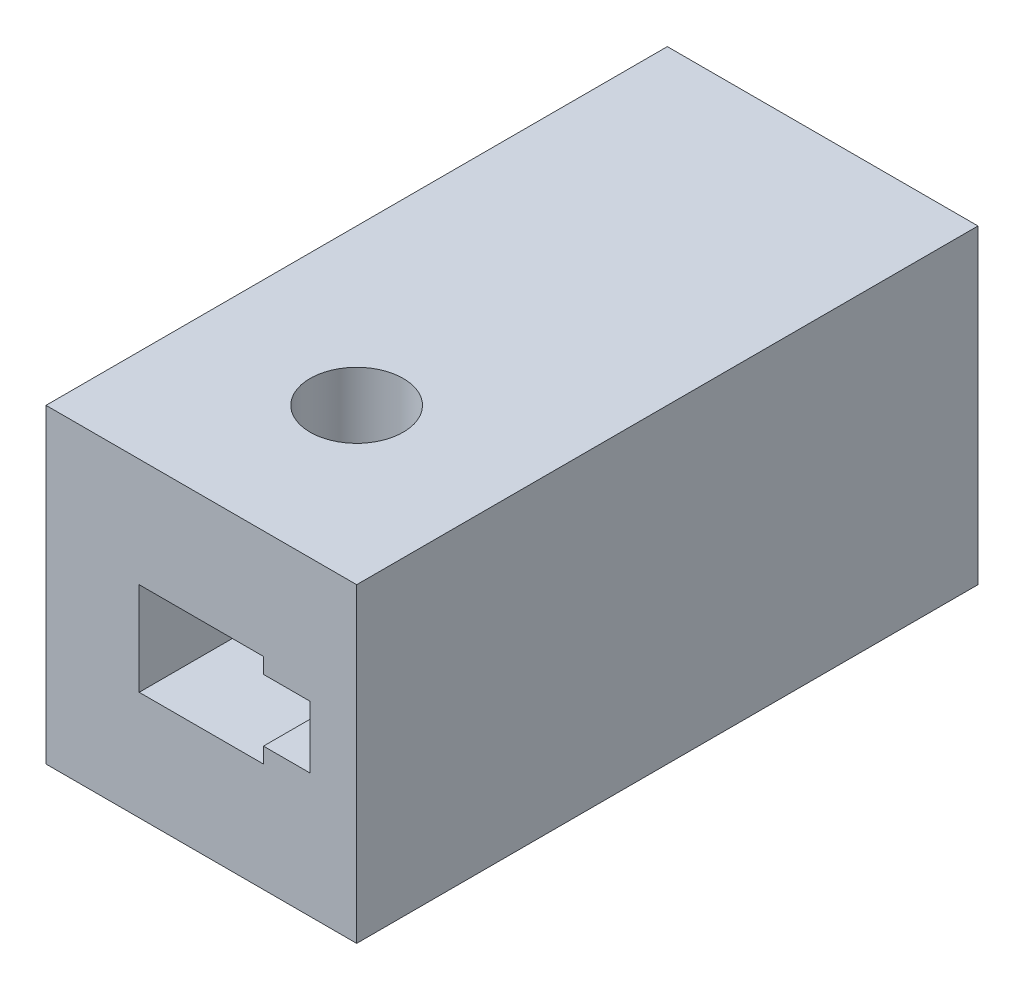
SolidWorks part; units mm, degrees
material "ABS"
ref_plane "Front Plane" through (0, 0, 0) normal (0, 0, 1) x (1, 0, 0)
ref_plane "Top Plane" through (0, 0, 0) normal (0, 1, 0) x (1, 0, 0)
ref_plane "Right Plane" through (0, 0, 0) normal (1, 0, 0) x (0, 0, -1)
sketch "Sketch1" plane through (0, 0, 0) normal (0, 0, 1) x (1, 0, 0)
  line L1 (-5, -5) -> (5, -5)
  line L2 (-5, -5) -> (-5, 5)
  line L3 (-5, 5) -> (5, 5)
  line L4 (5, -5) -> (5, 5)
  line L5 (-5, -5) -> (5, 5) construction
  line L6 (-5, 5) -> (5, -5) construction
  line L7 (-2, -1.5) -> (2, -1.5)
  line L8 (-2, -1.5) -> (-2, 1.5)
  line L9 (-2, 1.5) -> (2, 1.5)
  line L10 (2, -1.5) -> (2, 1.5)
  line L11 (-2, -1.5) -> (2, 1.5) construction
  line L12 (-2, 1.5) -> (2, -1.5) construction
  line L13 (2, -1) -> (3.5, -1)
  line L14 (2, -1) -> (2, 1)
  line L15 (2, 1) -> (3.5, 1)
  line L16 (3.5, -1) -> (3.5, 1)
  line L17 (2, -1) -> (3.5, 1) construction
  line L18 (2, 1) -> (3.5, -1) construction
  point P0 (0, 0)
  point P5 (0, 0)
  point P11 (2.75, 0)
  dimension "D1" = 10
  dimension "D2" = 10
  dimension "D3" = 4
  dimension "D4" = 3
  dimension "D5" = 2
  dimension "D6" = 1.5
  dimension "D7" = 0.75
  dimension "D8" = 1.5
extrude "Boss-Extrude1" add sketch "Sketch1" along normal blind 20 contours L1 L4 L3 L2 L16 L13 L10 L7 L8 L9 L15
sketch "Sketch2" plane through (0, -5, 0) normal (0, -1, 0) x (1, 0, 0)
  line L0 (-5, 20) -> (5, 20) construction
  circle A0 centre (0, 15) radius 1.5
  dimension "D1" = 3
  dimension "D2" = 5
extrude "Cut-Extrude1" cut sketch "Sketch2" against normal blind 20
sketch "Sketch3" plane through (0, 0, 0) normal (0, 0, -1) x (-1, 0, 0)
  line L1 (-5, -5) -> (5, -5)
  line L2 (-5, -5) -> (-5, 5)
  line L3 (-5, 5) -> (5, 5)
  line L4 (5, -5) -> (5, 5)
  line L5 (-5, -5) -> (5, 5) construction
  line L6 (-5, 5) -> (5, -5) construction
  point P0 (0, 0)
